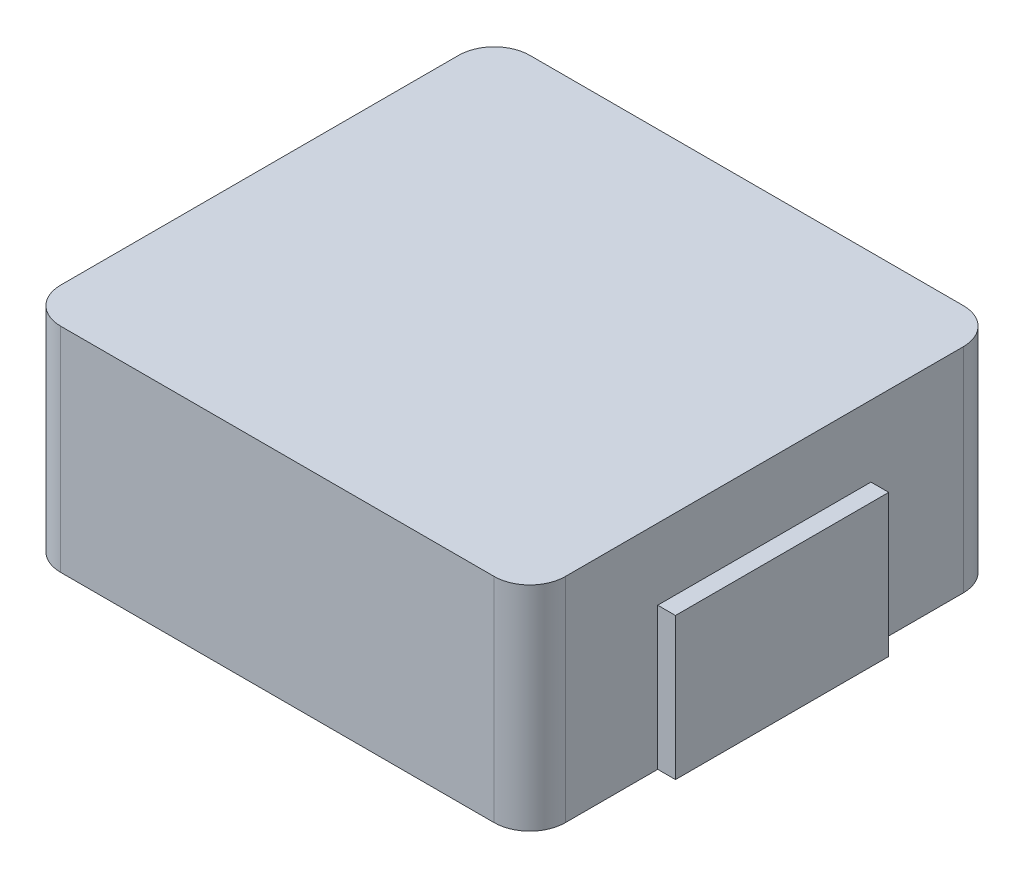
SolidWorks part; units mm, degrees
ref_plane "前视基准面" through (0, 0, 0) normal (0, 0, 1) x (1, 0, 0)
ref_plane "上视基准面" through (0, 0, 0) normal (0, 1, 0) x (1, 0, 0)
ref_plane "右视基准面" through (0, 0, 0) normal (1, 0, 0) x (0, 0, -1)
sketch "草图1" plane through (0, 0, 0) normal (0, 1, 0) x (1, 0, 0)
  line L1 (-3.55, -3.3) -> (3.55, -3.3)
  line L2 (-3.55, -3.3) -> (-3.55, 3.3)
  line L3 (-3.55, 3.3) -> (3.55, 3.3)
  line L4 (3.55, -3.3) -> (3.55, 3.3)
  line L5 (-3.55, -3.3) -> (3.55, 3.3) construction
  line L6 (-3.55, 3.3) -> (3.55, -3.3) construction
  point P0 (0, 0)
  dimension "D1" = 7.1
  dimension "D2" = 6.6
extrude "凸台-拉伸1" add sketch "草图1" along normal blind 3
fillet "圆角1" radius 0.5 4 edges at (-3.55, 1.5, -3.3) (3.55, 1.5, -3.3) (3.55, 1.5, 3.3) (-3.55, 1.5, 3.3)
sketch "草图2" plane through (0, 0, 0) normal (0, -1, 0) x (1, 0, 0)
  line L0 (0, -3.3) -> (0, 3.3) construction
  line L1 (3.05, -3.3) -> (-3.05, -3.3) construction
  line L2 (-3.05, 3.3) -> (3.05, 3.3) construction
  line L3 (0, 0) -> (3.55, 0) construction
  line L4 (3.55, 2.8) -> (3.55, -2.8) construction
  line L5 (-3.8, 1.5) -> (-3.8, -1.5)
  line L6 (3.3, 1.5) -> (3.8, 1.5)
  line L7 (3.3, 1.5) -> (3.3, -1.5)
  line L8 (3.3, -1.5) -> (3.8, -1.5)
  line L9 (3.8, 1.5) -> (3.8, -1.5)
  line L10 (3.3, 1.5) -> (3.8, -1.5) construction
  line L11 (3.3, -1.5) -> (3.8, 1.5) construction
  line L12 (-3.3, -1.5) -> (-3.8, -1.5)
  line L13 (-3.3, 1.5) -> (-3.3, -1.5)
  line L14 (-3.3, 1.5) -> (-3.8, 1.5)
  dimension "D1" = 3
  dimension "D2" = 0.5
extrude "凸台-拉伸2" add sketch "草图2" against normal blind 2
